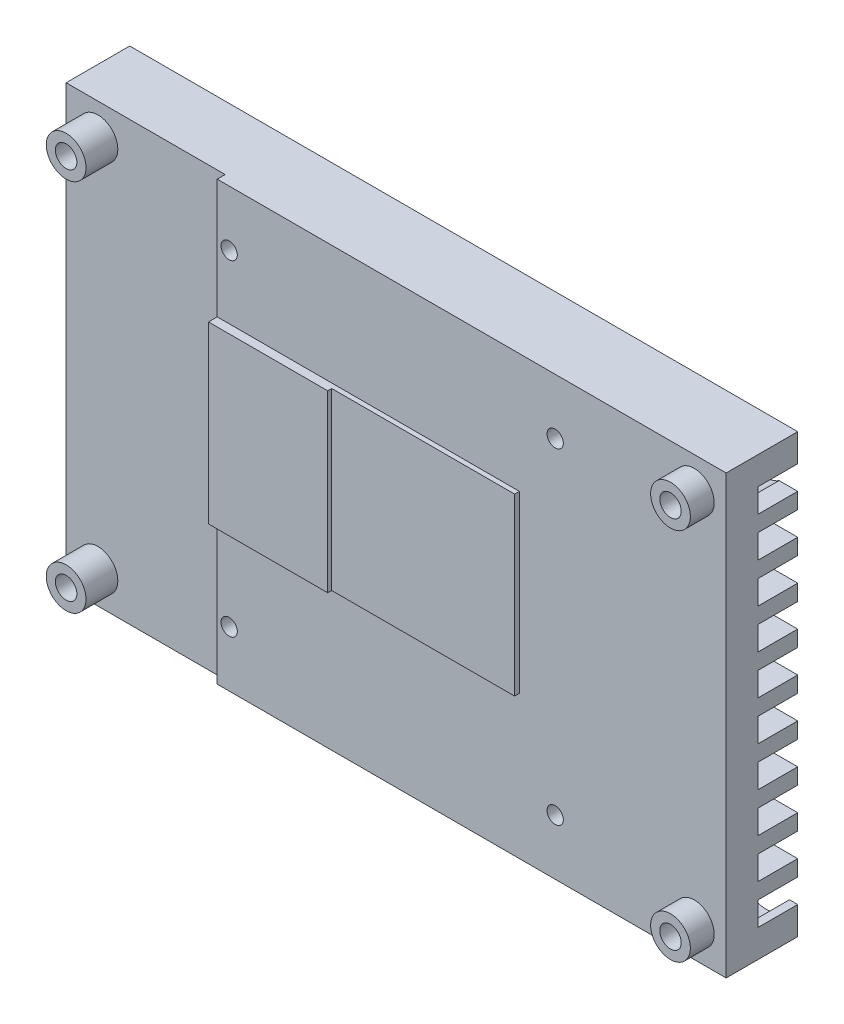
SolidWorks part; units mm, degrees
material "6061 Alloy"
ref_plane "Front Plane" through (0, 0, 0) normal (0, 0, 1) x (1, 0, 0)
ref_plane "Top Plane" through (0, 0, 0) normal (0, 1, 0) x (1, 0, 0)
ref_plane "Right Plane" through (0, 0, 0) normal (1, 0, 0) x (0, 0, -1)
sketch "Sketch1" plane through (0, 0, 0) normal (0, 0, 1) x (1, 0, 0)
  line L1 (-42, -27.5) -> (42, -27.5)
  line L2 (-42, -27.5) -> (-42, 27.5)
  line L3 (-42, 27.5) -> (42, 27.5)
  line L4 (42, -27.5) -> (42, 27.5)
  line L5 (-42, -27.5) -> (42, 27.5) construction
  line L6 (-42, 27.5) -> (42, -27.5) construction
  point P0 (0, 0)
  dimension "D1" = 84
  dimension "D2" = 55
extrude "Extrude1" add sketch "Sketch1" along normal blind 7
hole_wizard "Ø2.7 (2.7) Diameter Hole1" positions "Sketch3" profile "Sketch2" hole size "Ø2.7" standard "Ansi Metric" end condition through all
sketch "Sketch3" plane through (0, 0, 7) normal (0, 0, 1) x (1, 0, 0)
  line L0 (0, 23.3133) -> (0, -31.1405) construction
  line L2 (-36.022, 0) -> (46.2058, 0) construction
  point P0 (-38, 23.5)
  point P1 (38, 23.5)
  point P3 (38, -23.5)
  point P5 (-38, -23.5)
  dimension "D1" = 76
  dimension "D2" = 47
sketch "Sketch2" plane through (-38, 23.5, 7) normal (1, 0, 0) x (0, -1, 0)
  line L0 (0, 0) -> (0, 7)
  line L1 (0, 7) -> (1.35, 7)
  line L2 (1.35, 7) -> (1.35, 0)
  line L5 (1.35, 0) -> (0, 0)
  line L11 (0, -6.35) -> (0, 107.95) construction
  dimension "Thru Hole Dia." = 2.7
  dimension "Thru Hole Depth" = 7
sketch "Sketch6" plane through (0, 0, 7) normal (0, 0, 1) x (1, 0, 0)
  circle A0 centre (-38, 23.5) radius 2.5
  circle A1 centre (-38, -23.5) radius 2.5
  circle A2 centre (38, 23.5) radius 2.5
  circle A3 centre (38, -23.5) radius 2.5
  dimension "D1" = 5
extrude "Extrude2" cut sketch "Sketch6" against normal blind 3 flip side to cut
sketch "Sketch7" plane through (0, 0, 4) normal (0, 0, 1) x (1, 0, 0)
  line L1 (-22, 12.5) -> (-7, 12.5)
  line L2 (-22, 12.5) -> (-22, -9.5)
  line L3 (-22, -9.5) -> (-7, -9.5)
  line L4 (-7, 12.5) -> (-7, -9.5)
  line L6 (42, 27.5) -> (-42, 27.5) construction
  line L7 (-42, -27.5) -> (42, -27.5) construction
  line L8 (42, -27.5) -> (42, 27.5) construction
  line L9 (-42, 27.5) -> (-42, -27.5) construction
  dimension "D1" = 20
  dimension "D2" = 15
  dimension "D3" = 18
  dimension "D4" = 49
extrude "Extrude3" add sketch "Sketch7" along normal offset from surface (1.1 mm away) 1.9 up to face at (-36.65, 23.5, 7)
sketch "Sketch8" plane through (0, 0, 4) normal (0, 0, 1) x (1, 0, 0)
  line L0 (-22, -9.5) -> (-22, 12.5) construction
  line L1 (-48.4716, 30.1824) -> (-22, 30.1824)
  line L2 (-48.4716, 30.1824) -> (-48.4716, -32.3929)
  line L3 (-48.4716, -32.3929) -> (-22, -32.3929)
  line L4 (-22, 30.1824) -> (-22, -32.3929)
  circle A0 centre (-38, -23.5) radius 2.5 construction
  circle A1 centre (-38, 23.5) radius 2.5 construction
  circle A2 centre (-38, -23.5) radius 2.5
  circle A3 centre (-38, 23.5) radius 2.5
extrude "Extrude6" cut sketch "Sketch8" against normal offset from surface (1 mm away) 4 up to face at (-36.65, 23.5, 7)
sketch "Sketch9" plane through (0, 0, 4) normal (0, 0, 1) x (1, 0, 0)
  line L0 (-7, 12.5) -> (-7, -9.5) construction
  line L1 (-7, 12.5) -> (16, 12.5)
  line L2 (-7, 12.5) -> (-7, -9.5)
  line L3 (-7, -9.5) -> (16, -9.5)
  line L4 (16, 12.5) -> (16, -9.5)
  line L5 (-22, 12.5) -> (-7, 12.5) construction
  line L6 (-7, -9.5) -> (-22, -9.5) construction
  line L7 (42, -27.5) -> (42, 27.5) construction
  dimension "D1" = 26
extrude "Extrude7" add sketch "Sketch9" along normal offset from surface (0.6 mm away) 2.4 up to face at (-36.65, 23.5, 7)
hole_wizard "M2.5x0.45 Tapped Hole1" positions "Sketch5" profile "Sketch4" tap size "M2.5x0.45" standard "Ansi Metric" end condition through all
sketch "Sketch5" plane through (0, 0, 7) normal (0, 0, 1) x (1, 0, 0)
  line L2 (-20.5, 20.5) -> (20.5, 20.5) construction
  line L5 (-20.5, -20.5) -> (20.5, -20.5) construction
  line L10 (20.5, -20.5) -> (20.5, 20.5) construction
  line L12 (20.5, 0) -> (0, 0) construction
  line L14 (0, 20.5) -> (0, 0) construction
  point P0 (-20.5, 20.5)
  point P1 (20.5, 20.5)
  point P3 (20.5, -20.5)
  point P5 (-20.5, -20.5)
  dimension "D1" = 41
sketch "Sketch4" plane through (-20.5, 20.5, 7) normal (1, 0, 0) x (0, -1, 0)
  line L0 (0, 0) -> (0, 7)
  line L1 (0, 7) -> (1.025, 7)
  line L2 (1.025, 7) -> (1.025, 0)
  line L5 (1.025, 0) -> (0, 0)
  line L11 (0, -6.35) -> (0, 107.95) construction
  dimension "Thru Tap Drill Dia." = 2.05
  dimension "Thru Tap Drill Depth" = 7
cosmetic thread "Hole Thread1" parameters "D2"=2.5
cosmetic thread "Hole Thread2" parameters "D2"=2.5
cosmetic thread "Hole Thread3" parameters "D2"=2.5
cosmetic thread "Hole Thread4" parameters "D2"=2.5
sketch "Sketch14" plane through (0, 0, 0) normal (0, 0, -1) x (-1, 0, 0)
  line L0 (42, 27.5) -> (42, -27.5) construction
  line L1 (-42, -27.5) -> (42, -27.5)
  line L2 (-42, -27.5) -> (-42, 27.5)
  line L3 (-42, 27.5) -> (42, 27.5)
  line L4 (42, -27.5) -> (42, 27.5)
  line L5 (-42, 27.5) -> (42, 27.5) construction
  circle A0 centre (-38, 23.5) radius 3
  circle A1 centre (-20.5, 20.5) radius 3
  circle A2 centre (20.5, 20.5) radius 3
  circle A3 centre (38, 23.5) radius 3
  circle A4 centre (-38, -23.5) radius 3
  circle A5 centre (-20.5, -20.5) radius 3
  circle A6 centre (20.5, -20.5) radius 3
  circle A7 centre (38, -23.5) radius 3
  dimension "D1" = 6
extrude "Extrude12" add sketch "Sketch14" along normal offset from surface (5 mm away) 12 up to face at (39.35, -23.5, 7)
sketch "Sketch16" plane through (0, 0, -5) normal (0, 0, -1) x (-1, 0, 0)
  line L1 (-54.3561, -20.999) -> (50.9243, -20.999)
  line L2 (-54.3561, -20.999) -> (-54.3561, -23.999)
  line L3 (-54.3561, -23.999) -> (50.9243, -23.999)
  line L4 (50.9243, -20.999) -> (50.9243, -23.999)
  line L34 (-42, -27.5) -> (42, -27.5) construction
  line L35 (-54.3561, -15.999) -> (50.9243, -15.999)
  line L36 (-54.3561, -15.999) -> (-54.3561, -18.999)
  line L37 (-54.3561, -18.999) -> (50.9243, -18.999)
  line L38 (50.9243, -15.999) -> (50.9243, -18.999)
  line L39 (-54.3561, -10.999) -> (50.9243, -10.999)
  line L40 (-54.3561, -10.999) -> (-54.3561, -13.999)
  line L41 (-54.3561, -13.999) -> (50.9243, -13.999)
  line L42 (50.9243, -10.999) -> (50.9243, -13.999)
  line L43 (-54.3561, -5.999) -> (50.9243, -5.999)
  line L44 (-54.3561, -5.999) -> (-54.3561, -8.999)
  line L45 (-54.3561, -8.999) -> (50.9243, -8.999)
  line L46 (50.9243, -5.999) -> (50.9243, -8.999)
  line L47 (-54.3561, -0.999) -> (50.9243, -0.999)
  line L48 (-54.3561, -0.999) -> (-54.3561, -3.999)
  line L49 (-54.3561, -3.999) -> (50.9243, -3.999)
  line L50 (50.9243, -0.999) -> (50.9243, -3.999)
  line L51 (-54.3561, 4.001) -> (50.9243, 4.001)
  line L52 (-54.3561, 4.001) -> (-54.3561, 1.001)
  line L53 (-54.3561, 1.001) -> (50.9243, 1.001)
  line L54 (50.9243, 4.001) -> (50.9243, 1.001)
  line L55 (-54.3561, 9.001) -> (50.9243, 9.001)
  line L56 (-54.3561, 9.001) -> (-54.3561, 6.001)
  line L57 (-54.3561, 6.001) -> (50.9243, 6.001)
  line L58 (50.9243, 9.001) -> (50.9243, 6.001)
  line L59 (-54.3561, 14.001) -> (50.9243, 14.001)
  line L60 (-54.3561, 14.001) -> (-54.3561, 11.001)
  line L61 (-54.3561, 11.001) -> (50.9243, 11.001)
  line L62 (50.9243, 14.001) -> (50.9243, 11.001)
  line L63 (-54.3561, 19.001) -> (50.9243, 19.001)
  line L64 (-54.3561, 19.001) -> (-54.3561, 16.001)
  line L65 (-54.3561, 16.001) -> (50.9243, 16.001)
  line L66 (50.9243, 19.001) -> (50.9243, 16.001)
  line L67 (-54.3561, 24.001) -> (50.9243, 24.001)
  line L68 (-54.3561, 24.001) -> (-54.3561, 21.001)
  line L69 (-54.3561, 21.001) -> (50.9243, 21.001)
  line L70 (50.9243, 24.001) -> (50.9243, 21.001)
  dimension "D1" = 3
  dimension "D2" = 3.501
extrude "Extrude13" cut sketch "Sketch16" against normal offset from surface (5 mm away) 7 up to face at (-36.65, 23.5, 7)
sketch "Sketch17" [suppressed] plane through (0, 0, 0) normal (0, 0, -1) x (-1, 0, 0)
  line L0 (35.0421, 24.001) -> (-35.0421, 24.001) construction
  line L1 (-22, 24.001) -> (-19, 24.001)
  line L2 (-22, 24.001) -> (-22, 16.999)
  line L3 (-22, 16.999) -> (-19, 16.999)
  line L4 (-19, 24.001) -> (-19, 16.999)
  line L5 (-22, 24.001) -> (-19, 16.999) construction
  line L6 (-22, 16.999) -> (-19, 24.001) construction
  line L8 (19, 16.999) -> (22, 16.999)
  line L9 (19, 16.999) -> (19, 24.001)
  line L10 (19, 24.001) -> (22, 24.001)
  line L11 (22, 16.999) -> (22, 24.001)
  line L12 (19, 16.999) -> (22, 24.001) construction
  line L13 (19, 24.001) -> (22, 16.999) construction
  line L14 (-35.0418, -23.999) -> (35.0418, -23.999) construction
  line L15 (19, -17.001) -> (22, -17.001)
  line L16 (19, -17.001) -> (19, -23.999)
  line L17 (19, -23.999) -> (22, -23.999)
  line L18 (22, -17.001) -> (22, -23.999)
  line L19 (19, -17.001) -> (22, -23.999) construction
  line L20 (19, -23.999) -> (22, -17.001) construction
  line L22 (-22, -17.001) -> (-19, -17.001)
  line L23 (-22, -17.001) -> (-22, -23.999)
  line L24 (-22, -23.999) -> (-19, -23.999)
  line L25 (-19, -17.001) -> (-19, -23.999)
  line L26 (-22, -17.001) -> (-19, -23.999) construction
  line L27 (-22, -23.999) -> (-19, -17.001) construction
  point P0 (-20.5, 20.5)
  point P6 (20.5, 20.5)
  point P14 (20.5, -20.5)
  point P22 (-20.5, -20.5)
  dimension "D1" = 3
